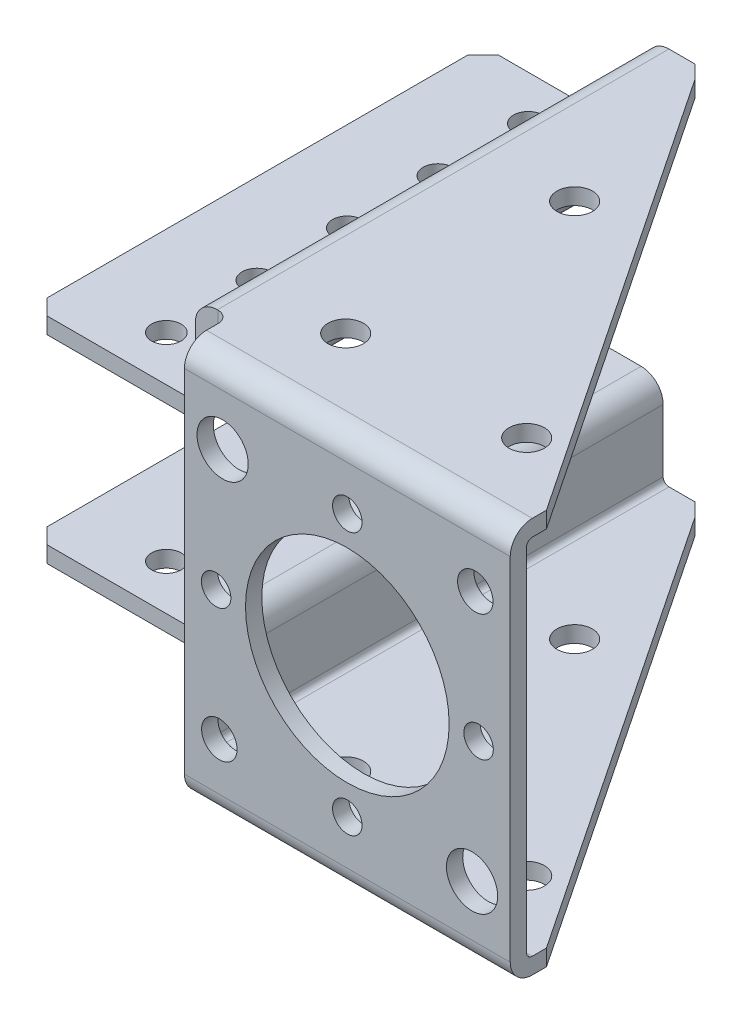
SolidWorks part; units mm, degrees
ref_plane "Front Plane" through (0, 0, 0) normal (0, 0, 1) x (1, 0, 0)
ref_plane "Top Plane" through (0, 0, 0) normal (0, 1, 0) x (1, 0, 0)
ref_plane "Right Plane" through (0, 0, 0) normal (1, 0, 0) x (0, 0, -1)
ref_plane "Plane1" through (0, 0, 2.286) normal (0, 0, 1) x (1, 0, 0)
sketch "Sketch1" plane through (0, 0, 2.286) normal (0, 0, 1) x (1, 0, 0)
  line L0 (22.86, -25.4635) -> (22.86, 25.4635)
  line L1 (22.86, 25.4635) -> (-20.32, 25.4635)
  line L2 (-20.32, 25.4635) -> (-20.32, -25.4635)
  line L3 (-20.32, -25.4635) -> (22.86, -25.4635)
extrude "Boss-Extrude1" add sketch "Sketch1" against normal blind 5.08
sketch "Sketch2" plane through (0, 25.4635, 0) normal (0, 1, 0) x (-1, 0, 0)
  line L0 (20.32, 2.286) -> (20.32, -67.437)
  line L1 (20.32, -67.437) -> (-22.86, -2.794)
  line L2 (-22.86, -2.794) -> (-22.86, 2.286)
  line L3 (-22.86, 2.286) -> (20.32, 2.286)
extrude "Boss-Extrude2" add sketch "Sketch2" along normal blind 2.286
sketch "Sketch3" plane through (0, -25.4635, 0) normal (0, -1, 0) x (1, 0, 0)
  line L0 (-20.32, -67.437) -> (-20.32, 2.286)
  line L1 (-20.32, 2.286) -> (22.86, 2.286)
  line L2 (22.86, 2.286) -> (22.86, -2.794)
  line L3 (22.86, -2.794) -> (-20.32, -67.437)
extrude "Boss-Extrude3" add sketch "Sketch3" along normal blind 2.286
sketch "Sketch4" plane through (0, 0, -2.794) normal (0, 0, -1) x (-1, 0, 0)
  line L0 (-22.86, -25.4635) -> (20.32, -25.4635)
  line L1 (20.32, -25.4635) -> (20.32, 25.4635)
  line L2 (20.32, 25.4635) -> (-22.86, 25.4635)
  line L3 (-22.86, 25.4635) -> (-22.86, -25.4635)
extrude "Cut-Extrude1" cut sketch "Sketch4" against normal blind 2.794
sketch "Sketch5" plane through (-20.32, 0, 0) normal (-1, 0, 0) x (0, 0, 1)
  line L0 (-67.437, -25.4635) -> (0, -25.4635)
  line L1 (0, -25.4635) -> (0, 25.4635)
  line L2 (0, 25.4635) -> (-67.437, 25.4635)
  line L3 (-67.437, 25.4635) -> (-67.437, 27.7495)
  line L4 (-67.437, 27.7495) -> (2.286, 27.7495)
  line L5 (2.286, 27.7495) -> (2.286, -27.7495)
  line L6 (2.286, -27.7495) -> (-67.437, -27.7495)
  line L7 (-67.437, -27.7495) -> (-67.437, -25.4635)
extrude "Boss-Extrude4" add sketch "Sketch5" along normal blind 2.54
sketch "Sketch6" plane through (-22.86, 0, 0) normal (-1, 0, 0) x (0, 0, 1)
  line L0 (-4.064, 25.4635) -> (-67.437, 25.4635)
  line L1 (-67.437, 25.4635) -> (-67.437, 27.7495)
  line L2 (-67.437, 27.7495) -> (-4.064, 27.7495)
  line L3 (-4.064, 27.7495) -> (-4.064, 25.4635)
extrude "Boss-Extrude5" add sketch "Sketch6" along normal blind 27.813
sketch "Sketch7" plane through (0, 25.4635, 0) normal (0, -1, 0) x (1, 0, 0)
  line L0 (-50.673, -67.437) -> (-50.673, -4.064)
  line L1 (-50.673, -4.064) -> (-25.4, -4.064)
  line L2 (-25.4, -4.064) -> (-25.4, -67.437)
  line L3 (-25.4, -67.437) -> (-50.673, -67.437)
extrude "Boss-Extrude6" add sketch "Sketch7" along normal blind 12.7
sketch "Sketch8" plane through (-22.86, 0, 0) normal (-1, 0, 0) x (0, 0, 1)
  line L0 (-67.437, -25.4635) -> (-4.064, -25.4635)
  line L1 (-4.064, -25.4635) -> (-4.064, -27.7495)
  line L2 (-4.064, -27.7495) -> (-67.437, -27.7495)
  line L3 (-67.437, -27.7495) -> (-67.437, -25.4635)
extrude "Boss-Extrude7" add sketch "Sketch8" along normal blind 27.813
sketch "Sketch9" plane through (0, -25.4635, 0) normal (0, 1, 0) x (-1, 0, 0)
  line L0 (50.673, -67.437) -> (25.4, -67.437)
  line L1 (25.4, -67.437) -> (25.4, -4.064)
  line L2 (25.4, -4.064) -> (50.673, -4.064)
  line L3 (50.673, -4.064) -> (50.673, -67.437)
extrude "Boss-Extrude8" add sketch "Sketch9" along normal blind 12.7
sketch "Sketch10" plane through (0, 0, -67.437) normal (0, 0, -1) x (-1, 0, 0)
  line L0 (27.686, 27.7495) -> (27.686, 15.0495)
  line L1 (27.686, 15.0495) -> (50.673, 15.0495)
  line L2 (50.673, 15.0495) -> (50.673, 27.7495)
  line L3 (50.673, 27.7495) -> (27.686, 27.7495)
extrude "Cut-Extrude2" cut sketch "Sketch10" against normal through all
sketch "Sketch11" plane through (0, 0, -67.437) normal (0, 0, -1) x (-1, 0, 0)
  line L0 (50.673, -27.7495) -> (50.673, -15.0495)
  line L1 (50.673, -15.0495) -> (27.686, -15.0495)
  line L2 (27.686, -15.0495) -> (27.686, -27.7495)
  line L3 (27.686, -27.7495) -> (50.673, -27.7495)
extrude "Cut-Extrude3" cut sketch "Sketch11" against normal through all
hole_wizard "Hole1" positions "Sketch13" profile "Sketch12" legacy
sketch "Sketch13" plane through (0, -27.7495, 0) normal (0, -1, 0) x (-1, 0, 0)
  point P0 (12.7, 10.1854)
  point P1 (-12.7, 10.1854)
  point P2 (12.7, 42.3164)
sketch "Sketch12" plane through (-12.7, -27.7495, -10.1854) normal (1, 0, 0) x (0, 0, -1)
  line L0 (0, 0) -> (0, 2.286)
  line L1 (0, 2.286) -> (2.4892, 2.286)
  line L2 (2.4892, 2.286) -> (2.4892, 0)
  line L3 (2.4892, 0) -> (0, 0)
  line L4 (0, 110) -> (0, -10) construction
  dimension "Diameter" = 4.9784
  dimension "Depth" = 2.286
hole_wizard "M3.5 Clearance Hole1" positions "Sketch15" profile "Sketch14" hole size "M3.5" standard "ANSI Metric"
sketch "Sketch15" plane through (0, 0, 2.286) normal (0, 0, 1) x (1, 0, 0)
  point P0 (0, -18.415)
sketch "Sketch14" plane through (0, -18.415, 2.286) normal (1, 0, 0) x (0, -1, 0)
  line L0 (0, 0) -> (0, 69.723)
  line L1 (0, 69.723) -> (2.0701, 69.723)
  line L2 (2.0701, 69.723) -> (2.0701, 0)
  line L5 (2.0701, 0) -> (0, 0)
  line L11 (0, -6.35) -> (0, 107.95) construction
  dimension "Thru Hole Dia." = 4.1402
  dimension "Thru Hole Depth" = 69.723
hole_wizard "M3.5 Clearance Hole2" positions "Sketch17" profile "Sketch16" hole size "M3.5" standard "ANSI Metric"
sketch "Sketch17" plane through (0, 0, 0) normal (0, 0, -1) x (-1, 0, 0)
  point P0 (-18.415, 0)
  point P1 (18.415, 0)
  point P2 (0, 18.415)
sketch "Sketch16" plane through (18.415, 0, 0) normal (1, 0, 0) x (0, 1, 0)
  line L0 (0, 0) -> (0, 2.286)
  line L1 (0, 2.286) -> (2.0701, 2.286)
  line L2 (2.0701, 2.286) -> (2.0701, 0)
  line L5 (2.0701, 0) -> (0, 0)
  line L11 (0, -6.35) -> (0, 107.95) construction
  dimension "Thru Hole Dia." = 4.1402
  dimension "Thru Hole Depth" = 2.286
hole_wizard "M25 Clearance Hole1" positions "Sketch19" profile "Sketch18" hole size "M25" standard "ANSI Metric"
sketch "Sketch19" plane through (0, 0, 0) normal (0, 0, -1) x (-1, 0, 0)
  point P0 (0, 0)
sketch "Sketch18" plane through (0, 0, 0) normal (1, 0, 0) x (0, 1, 0)
  line L0 (0, 0) -> (0, 2.286)
  line L1 (0, 2.286) -> (14.2875, 2.286)
  line L2 (14.2875, 2.286) -> (14.2875, 0)
  line L5 (14.2875, 0) -> (0, 0)
  line L11 (0, -6.35) -> (0, 107.95) construction
  dimension "Thru Hole Dia." = 28.575
  dimension "Thru Hole Depth" = 2.286
hole_wizard "M6.5 Clearance Hole1" positions "Sketch21" profile "Sketch20" hole size "M6.5" standard "ANSI Metric"
sketch "Sketch21" plane through (0, 0, 0) normal (0, 0, -1) x (-1, 0, 0)
  point P0 (17.5, 17.5)
  point P1 (-17.5, -17.5)
sketch "Sketch20" plane through (-17.5, 17.5, 0) normal (1, 0, 0) x (0, 1, 0)
  line L0 (0, 0) -> (0, 2.286)
  line L1 (0, 2.286) -> (3.5941, 2.286)
  line L2 (3.5941, 2.286) -> (3.5941, 0)
  line L5 (3.5941, 0) -> (0, 0)
  line L11 (0, -6.35) -> (0, 107.95) construction
  dimension "Thru Hole Dia." = 7.1882
  dimension "Thru Hole Depth" = 2.286
hole_wizard "Hole2" positions "Sketch23" profile "Sketch22" legacy
sketch "Sketch23" plane through (0, 0, 0) normal (0, 0, -1) x (-1, 0, 0)
  point P0 (17.9605, -17.9605)
  point P1 (-17.9605, 17.9605)
sketch "Sketch22" plane through (-17.9605, -17.9605, 0) normal (1, 0, 0) x (0, 1, 0)
  line L0 (0, 0) -> (0, 2.286)
  line L1 (0, 2.286) -> (2.4892, 2.286)
  line L2 (2.4892, 2.286) -> (2.4892, 0)
  line L3 (2.4892, 0) -> (0, 0)
  line L4 (0, 110) -> (0, -10) construction
  dimension "Diameter" = 4.9784
  dimension "Depth" = 2.286
hole_wizard "M3.5 Clearance Hole3" positions "Sketch25" profile "Sketch24" hole size "M3.5" standard "ANSI Metric"
sketch "Sketch25" plane through (0, -15.0495, 0) normal (0, -1, 0) x (-1, 0, 0)
  point P0 (38.1, 61.214)
  point P1 (38.1, 48.514)
  point P2 (38.1, 35.814)
  point P3 (38.1, 23.114)
  point P4 (38.1, 10.414)
sketch "Sketch24" plane through (-38.1, -15.0495, -61.214) normal (1, 0, 0) x (0, 0, -1)
  line L0 (0, 0) -> (0, 2.286)
  line L1 (0, 2.286) -> (2.0701, 2.286)
  line L2 (2.0701, 2.286) -> (2.0701, 0)
  line L5 (2.0701, 0) -> (0, 0)
  line L11 (0, -6.35) -> (0, 107.95) construction
  dimension "Thru Hole Dia." = 4.1402
  dimension "Thru Hole Depth" = 2.286
hole_wizard "Hole3" positions "Sketch27" profile "Sketch26" legacy
sketch "Sketch27" plane through (0, 25.4635, 0) normal (0, -1, 0) x (-1, 0, 0)
  point P0 (12.7, 10.1854)
  point P1 (-12.7, 10.1854)
  point P2 (12.7, 42.3164)
sketch "Sketch26" plane through (-12.7, 25.4635, -10.1854) normal (1, 0, 0) x (0, 0, -1)
  line L0 (0, 0) -> (0, 2.2861)
  line L1 (0, 2.2861) -> (2.4892, 2.2861)
  line L2 (2.4892, 2.2861) -> (2.4892, 0)
  line L3 (2.4892, 0) -> (0, 0)
  line L4 (0, 110) -> (0, -10) construction
  dimension "Diameter" = 4.9784
  dimension "Depth" = 2.2861
hole_wizard "M3.5 Clearance Hole4" positions "Sketch29" profile "Sketch28" hole size "M3.5" standard "ANSI Metric"
sketch "Sketch29" plane through (0, 12.7635, 0) normal (0, -1, 0) x (-1, 0, 0)
  point P0 (38.1, 61.214)
  point P1 (38.1, 48.514)
  point P2 (38.1, 35.814)
  point P3 (38.1, 23.114)
  point P4 (38.1, 10.414)
sketch "Sketch28" plane through (-38.1, 12.7635, -61.214) normal (1, 0, 0) x (0, 0, -1)
  line L0 (0, 0) -> (0, 14.9861)
  line L1 (0, 14.9861) -> (2.0701, 14.9861)
  line L2 (2.0701, 14.9861) -> (2.0701, 0)
  line L5 (2.0701, 0) -> (0, 0)
  line L11 (0, -6.35) -> (0, 107.95) construction
  dimension "Thru Hole Dia." = 4.1402
  dimension "Thru Hole Depth" = 14.9861
chamfer "Chamfer1" distance 0.5961 angle 45 1 edges at (-20.32, 26.6065, -67.437)
chamfer "Chamfer2" distance 2.159 angle 45 4 edges at (-50.673, -13.9065, -4.064) (-50.673, -13.9065, -67.437) (-50.673, 13.9065, -67.437) (-50.673, 13.9065, -4.064)
chamfer "Chamfer3" distance 2.159 angle 11.258 1 edges at (-20.32, -26.6065, -67.437)
fillet "Fillet1" radius 0.8128 6 edges at (0, -25.4635, 0) (-25.4, 25.4635, -35.7505) (-25.4, -25.4635, -35.7505) (-27.686, -15.0495, -35.7505) (-27.686, 15.0495, -35.7505) (0, 25.4635, 0)
fillet "Fillet2" radius 1.6256 2 edges at (-22.86, -26.6065, -4.064)
fillet "Fillet3" radius 3.0988 6 edges at (0, 27.7495, 2.286) (-27.686, -27.7495, -35.7505) (0, -27.7495, 2.286) (-25.4, 12.7635, -35.7505) (-25.4, -12.7635, -35.7505) (-27.686, 27.7495, -35.7505)
